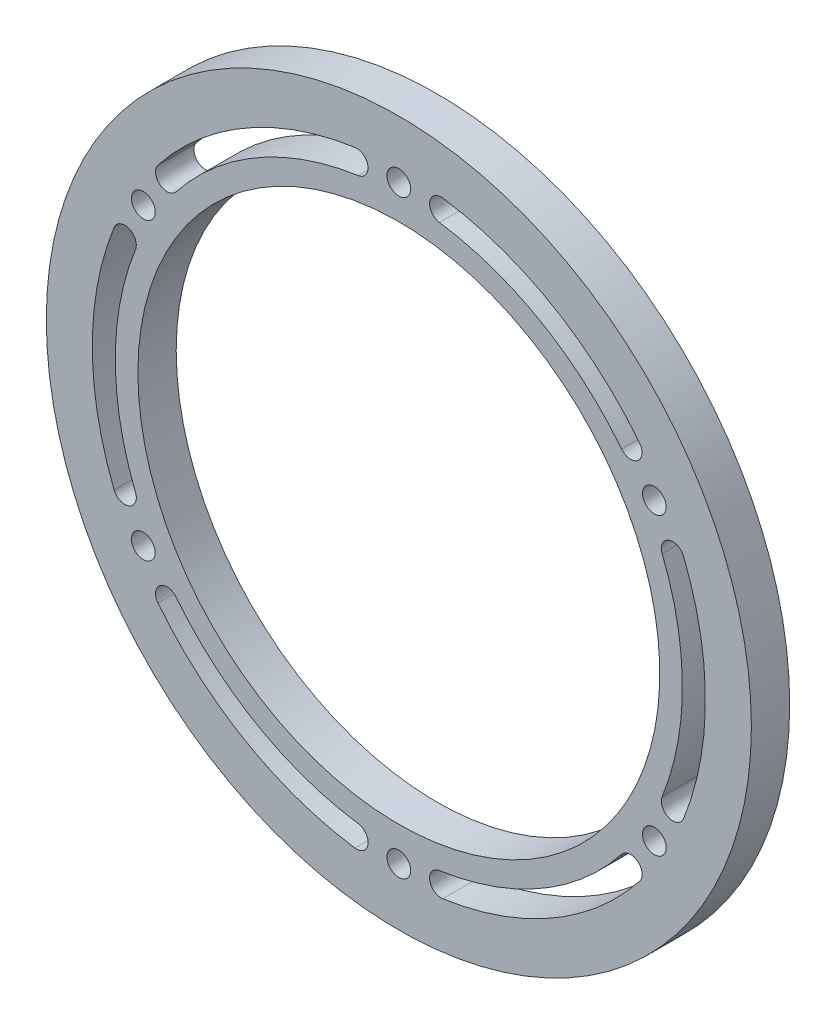
SolidWorks part; units mm, degrees
ref_plane "前视基准面" through (0, 0, 0) normal (0, 0, 1) x (1, 0, 0)
ref_plane "上视基准面" through (0, 0, 0) normal (0, 1, 0) x (1, 0, 0)
ref_plane "右视基准面" through (0, 0, 0) normal (1, 0, 0) x (0, 0, -1)
ref_plane "基准面4" through (0, 0, 2.5) normal (0, 0, 1) x (1, 0, 0)
sketch "草图1" plane through (0, 0, 2.5) normal (0, 0, 1) x (1, 0, 0)
  arc A0 (-5.2983, 36.6187) -> (-29.0636, 22.8978) centre (0, 0) ccw
  arc A1 (-29.0636, 22.8978) -> (-31.4201, 24.7544) centre (-30.2418, 23.8261) cw
  arc A2 (-31.4201, 24.7544) -> (-5.7279, 39.5878) centre (0, 0) cw
  arc A3 (-5.7279, 39.5878) -> (-5.2983, 36.6187) centre (-5.5131, 38.1032) cw
  arc A4 (29.0636, 22.8978) -> (5.2983, 36.6187) centre (0, 0) ccw
  arc A5 (5.2983, 36.6187) -> (5.7279, 39.5878) centre (5.5131, 38.1032) cw
  arc A6 (5.7279, 39.5878) -> (31.4201, 24.7544) centre (0, 0) cw
  arc A7 (31.4201, 24.7544) -> (29.0636, 22.8978) centre (30.2418, 23.8261) cw
  arc A8 (34.3619, -13.7209) -> (34.3619, 13.7209) centre (0, 0) ccw
  arc A9 (34.3619, 13.7209) -> (37.1479, 14.8334) centre (35.7549, 14.2772) cw
  arc A10 (37.1479, 14.8334) -> (37.1479, -14.8334) centre (0, 0) cw
  arc A11 (37.1479, -14.8334) -> (34.3619, -13.7209) centre (35.7549, -14.2772) cw
  arc A12 (5.2983, -36.6187) -> (29.0636, -22.8978) centre (0, 0) ccw
  arc A13 (29.0636, -22.8978) -> (31.4201, -24.7544) centre (30.2418, -23.8261) cw
  arc A14 (31.4201, -24.7544) -> (5.7279, -39.5878) centre (0, 0) cw
  arc A15 (5.7279, -39.5878) -> (5.2983, -36.6187) centre (5.5131, -38.1032) cw
  arc A16 (-29.0636, -22.8978) -> (-5.2983, -36.6187) centre (0, 0) ccw
  arc A17 (-5.2983, -36.6187) -> (-5.7279, -39.5878) centre (-5.5131, -38.1032) cw
  arc A18 (-5.7279, -39.5878) -> (-31.4201, -24.7544) centre (0, 0) cw
  arc A19 (-31.4201, -24.7544) -> (-29.0636, -22.8978) centre (-30.2418, -23.8261) cw
  arc A20 (-34.3619, 13.7209) -> (-34.3619, -13.7209) centre (0, 0) ccw
  arc A21 (-34.3619, -13.7209) -> (-37.1479, -14.8334) centre (-35.7549, -14.2772) cw
  arc A22 (-37.1479, -14.8334) -> (-37.1479, 14.8334) centre (0, 0) cw
  arc A23 (-37.1479, 14.8334) -> (-34.3619, 13.7209) centre (-35.7549, 14.2772) cw
  circle A24 centre (33.342, 19.25) radius 1.55
  circle A25 centre (33.342, -19.25) radius 1.55
  circle A26 centre (0, -38.5) radius 1.55
  circle A27 centre (-33.342, -19.25) radius 1.55
  circle A28 centre (-33.342, 19.25) radius 1.55
  circle A29 centre (0, 38.5) radius 1.55
  circle A30 centre (0, 0) radius 34.05
  circle A31 centre (0, 0) radius 46
extrude "凸台-拉伸1" add sketch "草图1" against normal blind 5
